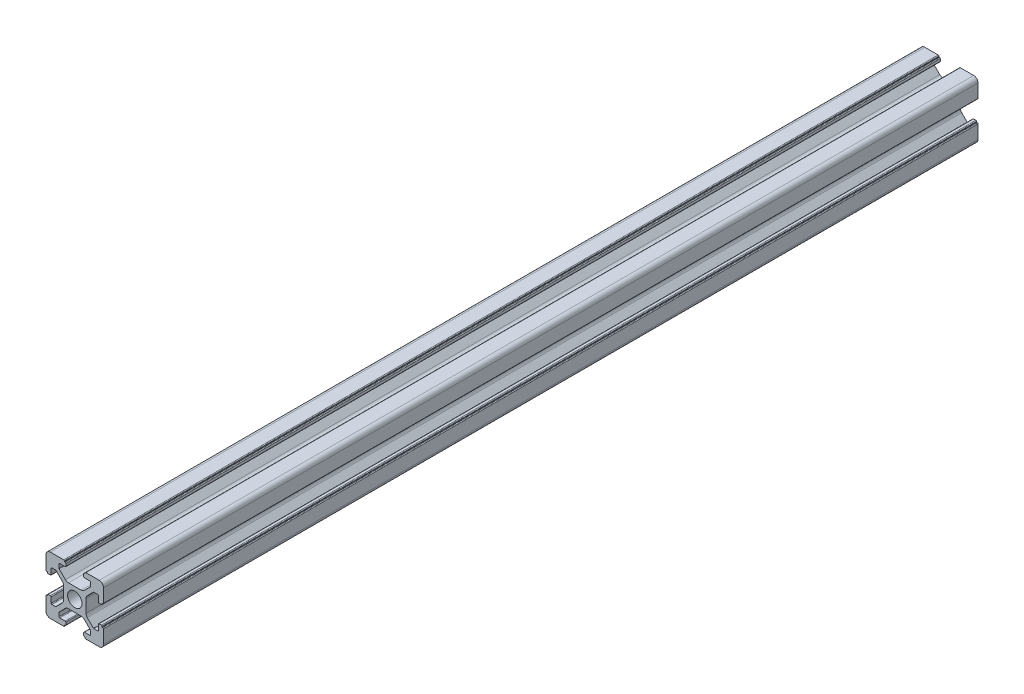
SolidWorks part; units mm, degrees
ref_plane "前视基准面" through (0, 0, 0) normal (0, 0, 1) x (1, 0, 0)
ref_plane "上视基准面" through (0, 0, 0) normal (0, 1, 0) x (1, 0, 0)
ref_plane "右视基准面" through (0, 0, 0) normal (1, 0, 0) x (0, 0, -1)
sketch "草图1" plane through (0, 0, 0) normal (0, 0, 1) x (1, 0, 0)
  line L0 (0, 0) -> (0, 5.5) construction
  line L1 (-8.5023, -10.0023) -> (-3.85, -10.0023)
  line L2 (-10.0023, -8.5023) -> (-10.0023, -3.85)
  line L3 (-8.5023, 10.0023) -> (-3.85, 10.0023)
  line L4 (10.0023, -8.5023) -> (10.0023, -3.85)
  line L5 (-10.0023, -10.0023) -> (10.0023, 10.0023) construction
  line L6 (-10.0023, 10.0023) -> (10.0023, -10.0023) construction
  line L7 (-2.218, -3.9) -> (2.218, -3.9)
  line L8 (-3.9, -2.218) -> (-3.9, 2.218)
  line L9 (-2.218, 3.9) -> (2.218, 3.9)
  line L10 (3.9, -2.218) -> (3.9, 2.218)
  line L11 (-3.9, -3.9) -> (3.9, 3.9) construction
  line L12 (-3.9, 3.9) -> (3.9, -3.9) construction
  line L13 (-5.25, -8.2) -> (-3.35, -8.2)
  line L14 (-8.2, -5.25) -> (-8.2, -3.35)
  line L15 (-5.25, 8.2) -> (-3.35, 8.2)
  line L16 (8.2, -5.25) -> (8.2, -3.35)
  line L17 (-8.2, -8.2) -> (8.2, 8.2) construction
  line L18 (-8.2, 8.2) -> (8.2, -8.2) construction
  line L19 (-7.95, 5.5) -> (-6.6642, 5.5)
  line L20 (0, 0) -> (5.5, 0) construction
  line L23 (-5.5, 7.95) -> (-5.5, 6.6642)
  line L26 (0, 0) -> (-0.5303, 0.5303)
  line L27 (3.2787, 4.3393) -> (5.4268, 6.4874)
  line L28 (0, 0) -> (0.5303, -0.5303)
  line L29 (5.5, 6.6642) -> (5.5, 7.95)
  line L30 (4.3393, 3.2787) -> (6.4874, 5.4268)
  line L31 (6.6642, 5.5) -> (7.95, 5.5)
  line L32 (4.3393, -3.2787) -> (6.4874, -5.4268)
  line L33 (3.2787, -4.3393) -> (5.4268, -6.4874)
  line L34 (-3.2787, -4.3393) -> (-5.4268, -6.4874)
  line L35 (-4.3393, -3.2787) -> (-6.4874, -5.4268)
  line L36 (-4.3393, 3.2787) -> (-6.4874, 5.4268)
  line L37 (-3.2787, 4.3393) -> (-5.4268, 6.4874)
  line L38 (3.1, -8.45) -> (3.1, -9.2523)
  line L39 (8.45, 3.1) -> (9.2523, 3.1)
  line L40 (-5.5, -6.6642) -> (-5.5, -7.95)
  line L41 (-6.6642, -5.5) -> (-7.95, -5.5)
  line L42 (5.5, -6.6642) -> (5.5, -7.95)
  line L43 (6.6642, -5.5) -> (7.95, -5.5)
  line L44 (9.2523, -3.1) -> (8.45, -3.1)
  line L46 (10.0023, 3.85) -> (10.0023, 8.5023)
  line L47 (8.2, 3.35) -> (8.2, 5.25)
  line L48 (-3.1, -9.2523) -> (-3.1, -8.45)
  line L49 (-8.45, -3.1) -> (-9.2523, -3.1)
  line L50 (-9.2523, 3.1) -> (-8.45, 3.1)
  line L51 (-3.1, 8.45) -> (-3.1, 9.2523)
  line L52 (3.1, 9.2523) -> (3.1, 8.45)
  line L53 (3.85, 10.0023) -> (8.5023, 10.0023)
  line L54 (3.35, 8.2) -> (5.25, 8.2)
  line L55 (-10.0023, 3.85) -> (-10.0023, 8.5023)
  line L56 (-8.2, 3.35) -> (-8.2, 5.25)
  line L57 (3.35, -8.2) -> (5.25, -8.2)
  line L58 (3.85, -10.0023) -> (8.5023, -10.0023)
  line L59 (9.7523, -3.6) -> (9.5023, -3.6)
  line L61 (9.7523, 3.6) -> (9.5023, 3.6)
  line L62 (9.5023, -3.6) -> (9.5023, -3.35)
  line L63 (3.6, -9.7523) -> (3.6, -9.5023)
  line L64 (3.35, -9.5023) -> (3.6, -9.5023)
  line L65 (9.5023, 3.35) -> (9.5023, 3.6)
  line L66 (-3.6, -9.5023) -> (-3.35, -9.5023)
  line L67 (-3.6, -9.7523) -> (-3.6, -9.5023)
  line L68 (-9.7523, -3.6) -> (-9.5023, -3.6)
  line L69 (-9.5023, -3.35) -> (-9.5023, -3.6)
  line L70 (-9.5023, 3.6) -> (-9.5023, 3.35)
  line L71 (-9.7523, 3.6) -> (-9.5023, 3.6)
  line L72 (-3.6, 9.7523) -> (-3.6, 9.5023)
  line L73 (-3.35, 9.5023) -> (-3.6, 9.5023)
  line L74 (3.6, 9.5023) -> (3.35, 9.5023)
  line L75 (3.6, 9.7523) -> (3.6, 9.5023)
  circle A0 centre (0, 0) radius 2.5
  arc A1 (10.0023, 8.5023) -> (8.5023, 10.0023) centre (8.5023, 8.5023) ccw
  arc A2 (8.5023, -10.0023) -> (10.0023, -8.5023) centre (8.5023, -8.5023) ccw
  arc A3 (-10.0023, -8.5023) -> (-8.5023, -10.0023) centre (-8.5023, -8.5023) ccw
  arc A4 (-10.0023, 8.5023) -> (-8.5023, 10.0023) centre (-8.5023, 8.5023) cw
  arc A5 (-9.5023, -3.35) -> (-9.2523, -3.1) centre (-9.2523, -3.35) cw
  arc A6 (-9.7523, -3.6) -> (-10.0023, -3.85) centre (-9.7523, -3.85) ccw
  arc A7 (-8.45, -3.1) -> (-8.2, -3.35) centre (-8.45, -3.35) cw
  arc A8 (-7.95, -5.5) -> (-8.2, -5.25) centre (-7.95, -5.25) cw
  arc A9 (-6.4874, -5.4268) -> (-6.6642, -5.5) centre (-6.6642, -5.25) cw
  arc A10 (-5.4268, -6.4874) -> (-5.5, -6.6642) centre (-5.25, -6.6642) ccw
  arc A11 (-5.5, -7.95) -> (-5.25, -8.2) centre (-5.25, -7.95) ccw
  arc A12 (-3.6, -9.7523) -> (-3.85, -10.0023) centre (-3.85, -9.7523) cw
  arc A13 (-3.35, -9.5023) -> (-3.1, -9.2523) centre (-3.35, -9.2523) ccw
  arc A14 (-3.1, -8.45) -> (-3.35, -8.2) centre (-3.35, -8.45) ccw
  arc A15 (3.1, -8.45) -> (3.35, -8.2) centre (3.35, -8.45) cw
  arc A16 (5.5, -7.95) -> (5.25, -8.2) centre (5.25, -7.95) cw
  arc A17 (5.4268, -6.4874) -> (5.5, -6.6642) centre (5.25, -6.6642) cw
  arc A18 (6.4874, -5.4268) -> (6.6642, -5.5) centre (6.6642, -5.25) ccw
  arc A19 (7.95, -5.5) -> (8.2, -5.25) centre (7.95, -5.25) ccw
  arc A20 (8.45, -3.1) -> (8.2, -3.35) centre (8.45, -3.35) ccw
  arc A21 (9.5023, -3.35) -> (9.2523, -3.1) centre (9.2523, -3.35) ccw
  arc A22 (9.7523, -3.6) -> (10.0023, -3.85) centre (9.7523, -3.85) cw
  arc A23 (3.35, -9.5023) -> (3.1, -9.2523) centre (3.35, -9.2523) cw
  arc A24 (3.6, -9.7523) -> (3.85, -10.0023) centre (3.85, -9.7523) ccw
  arc A25 (7.95, 5.5) -> (8.2, 5.25) centre (7.95, 5.25) cw
  arc A26 (8.2, 3.35) -> (8.45, 3.1) centre (8.45, 3.35) ccw
  arc A27 (9.5023, 3.35) -> (9.2523, 3.1) centre (9.2523, 3.35) cw
  arc A28 (9.7523, 3.6) -> (10.0023, 3.85) centre (9.7523, 3.85) ccw
  arc A29 (6.6642, 5.5) -> (6.4874, 5.4268) centre (6.6642, 5.25) ccw
  arc A30 (5.4268, 6.4874) -> (5.5, 6.6642) centre (5.25, 6.6642) ccw
  arc A31 (5.5, 7.95) -> (5.25, 8.2) centre (5.25, 7.95) ccw
  arc A32 (3.1, 8.45) -> (3.35, 8.2) centre (3.35, 8.45) ccw
  arc A33 (3.6, 9.7523) -> (3.85, 10.0023) centre (3.85, 9.7523) cw
  arc A34 (3.35, 9.5023) -> (3.1, 9.2523) centre (3.35, 9.2523) ccw
  arc A35 (-9.7523, 3.6) -> (-10.0023, 3.85) centre (-9.7523, 3.85) cw
  arc A36 (-9.5023, 3.35) -> (-9.2523, 3.1) centre (-9.2523, 3.35) ccw
  arc A37 (-8.45, 3.1) -> (-8.2, 3.35) centre (-8.45, 3.35) ccw
  arc A38 (-8.2, 5.25) -> (-7.95, 5.5) centre (-7.95, 5.25) cw
  arc A39 (-6.4874, 5.4268) -> (-6.6642, 5.5) centre (-6.6642, 5.25) ccw
  arc A40 (-5.4268, 6.4874) -> (-5.5, 6.6642) centre (-5.25, 6.6642) cw
  arc A41 (-5.5, 7.95) -> (-5.25, 8.2) centre (-5.25, 7.95) cw
  arc A42 (-3.1, 8.45) -> (-3.35, 8.2) centre (-3.35, 8.45) cw
  arc A43 (-3.1, 9.2523) -> (-3.35, 9.5023) centre (-3.35, 9.2523) ccw
  arc A44 (-3.6, 9.7523) -> (-3.85, 10.0023) centre (-3.85, 9.7523) ccw
  arc A45 (-4.3393, 3.2787) -> (-3.9, 2.218) centre (-5.4, 2.218) cw
  arc A46 (-3.2787, 4.3393) -> (-2.218, 3.9) centre (-2.218, 5.4) ccw
  arc A47 (3.2787, 4.3393) -> (2.218, 3.9) centre (2.218, 5.4) cw
  arc A48 (4.3393, 3.2787) -> (3.9, 2.218) centre (5.4, 2.218) ccw
  arc A49 (4.3393, -3.2787) -> (3.9, -2.218) centre (5.4, -2.218) cw
  arc A50 (3.2787, -4.3393) -> (2.218, -3.9) centre (2.218, -5.4) ccw
  arc A51 (-4.3393, -3.2787) -> (-3.9, -2.218) centre (-5.4, -2.218) ccw
  arc A52 (-2.218, -3.9) -> (-3.2787, -4.3393) centre (-2.218, -5.4) ccw
  point P0 (0, 0)
  point P7 (10.0023, 0)
  point P62 (0, 0)
  point P76 (0, 0)
  point P92 (-8.2, -5.5)
  point P99 (0, 0)
  point P106 (-5.5, -8.2)
  point P117 (5.5, -8.2)
  point P124 (8.2, -5.5)
  point P137 (8.2, 5.5)
  point P140 (8.2, 3.1)
  point P147 (6.5607, 5.5)
  point P152 (5.5, 8.2)
  point P167 (-8.2, 5.5)
  point P174 (-5.5, 8.2)
  dimension "D1" = 1.5
  dimension "D5" = 0.25
  dimension "D6" = 1.5
  dimension "D2" = 4
  dimension "D3" = 4
  dimension "D4" = 4
extrude "凸台-拉伸1" add sketch "草图1" along normal blind 304 contours A52 L7 A50 L33 A17 L42 A16 L57 A15 L38 A23 L64 L63 A24 L58 A2 L4 A22 L59 L62 A21 L44 A20 L16 A19 L43 A18 L32 A49 L10 A48 L30 A29 L31 A25 L47 A26 L39 A27 L65 L61 A28 L46 A1 L53 A33 L75 L74 A34 L52 A32
ref_plane "Plane1" through (0, 0, 152) normal (0, 0, 1) x (1, 0, 0)
